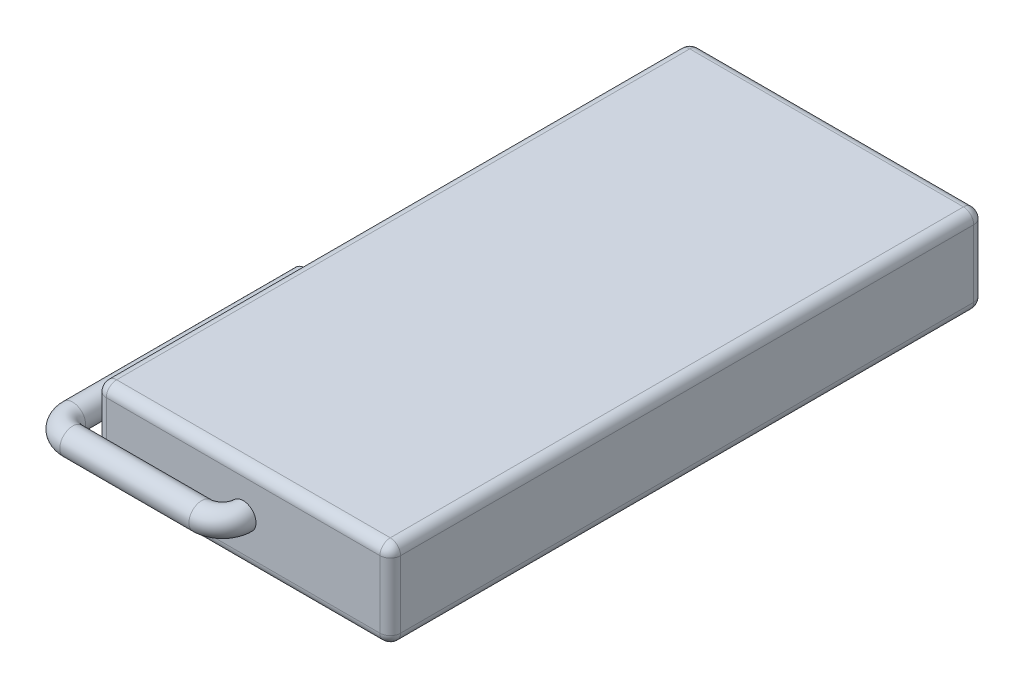
SolidWorks part; units mm, degrees
ref_plane "前视基准面" through (0, 0, 0) normal (0, 0, 1) x (1, 0, 0)
ref_plane "上视基准面" through (0, 0, 0) normal (0, 1, 0) x (1, 0, 0)
ref_plane "右视基准面" through (0, 0, 0) normal (1, 0, 0) x (0, 0, -1)
sketch "草图1" plane through (0, 0, 0) normal (0, 1, 0) x (1, 0, 0)
  line L1 (28.5, -57.5) -> (-28.5, -57.5)
  line L2 (28.5, -57.5) -> (28.5, 57.5)
  line L3 (28.5, 57.5) -> (-28.5, 57.5)
  line L4 (-28.5, -57.5) -> (-28.5, 57.5)
  line L5 (28.5, -57.5) -> (-28.5, 57.5) construction
  line L6 (28.5, 57.5) -> (-28.5, -57.5) construction
  point P0 (0, 0)
  dimension "D1" = 57
  dimension "D2" = 115
extrude "凸台-拉伸1" add sketch "草图1" along normal mid plane 17
fillet "圆角1" radius 2 12 edges at (28.5, -8.5, 0) (28.5, 8.5, 0) (28.5, 0, -57.5) (0, 8.5, -57.5) (0, -8.5, -57.5) (-28.5, 0, -57.5) (-28.5, 8.5, 0) (-28.5, -8.5, 0) (-28.5, 0, 57.5) (0, 8.5, 57.5) (28.5, 0, 57.5) (0, -8.5, 57.5)
sketch "草图2" plane through (0, 0, 0) normal (0, 1, 0) x (1, 0, 0)
  line L0 (0, -55.5) -> (0, -57.5) construction
  line L1 (-26.5, -55.5) -> (26.5, -55.5) construction
  line L2 (26.5, -57.5) -> (-26.5, -57.5) construction
  line L3 (-4, -61.5) -> (-29, -61.5)
  line L4 (-33, -57.5) -> (-33, -12.5)
  arc A0 (0, -57.5) -> (-4, -61.5) centre (-4, -57.5) cw
  arc A1 (-29, -61.5) -> (-33, -57.5) centre (-29, -57.5) cw
  dimension "D1" = 4
  dimension "D3" = 4
  dimension "D2" = 25
  dimension "D4" = 45
sketch "草图3" plane through (0, 0, 57.5) normal (0, 0, 1) x (1, 0, 0)
  circle A0 centre (0, 0) radius 2.5
  dimension "D1" = 5
sweep "扫描1" add profiles "草图3" path "草图2"
